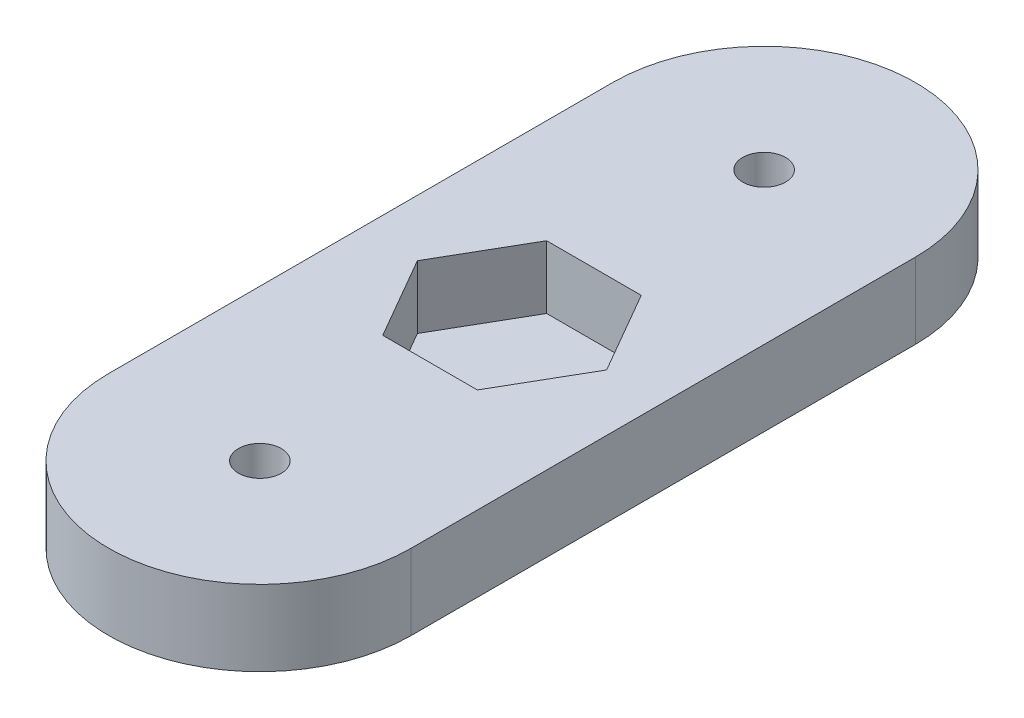
SolidWorks part; units mm, degrees
material "ABS PC"
ref_plane "Front Plane" through (0, 0, 0) normal (0, 0, 1) x (1, 0, 0)
ref_plane "Top Plane" through (0, 0, 0) normal (0, 1, 0) x (1, 0, 0)
ref_plane "Right Plane" through (0, 0, 0) normal (1, 0, 0) x (0, 0, -1)
sketch "Sketch1" plane through (0, 0, 0) normal (0, 1, 0) x (1, 0, 0)
  line L0 (0, 0) -> (0, 40) construction
  line L1 (-12, 0) -> (-12, 40)
  line L2 (12, 0) -> (12, 40)
  arc A0 (-12, 0) -> (12, 0) centre (0, 0) ccw
  arc A1 (12, 40) -> (-12, 40) centre (0, 40) ccw
  circle A2 centre (0, 40) radius 1.7
  circle A3 centre (0, 0) radius 1.7
  point P3 (0, 20)
  dimension "D2" = 40
  dimension "D3" = 3.4
  dimension "D1" = 24
extrude "Boss-Extrude1" add sketch "Sketch1" along normal blind 6
sketch "Sketch2" plane through (0, 6, 0) normal (0, 1, 0) x (1, 0, 0)
  line L0 (12, 0) -> (12, 40) construction
  line L1 (3.7528, 13.5) -> (7.5056, 20)
  line L2 (7.5056, 20) -> (3.7528, 26.5)
  line L3 (3.7528, 26.5) -> (-3.7528, 26.5)
  line L4 (-3.7528, 26.5) -> (-7.5056, 20)
  line L5 (-7.5056, 20) -> (-3.7528, 13.5)
  line L6 (-3.7528, 13.5) -> (3.7528, 13.5)
  line L7 (-12, 40) -> (-12, 0) construction
  circle A0 centre (0, 20) radius 6.5 construction
  dimension "D1" = 13
  dimension "D2" = 12
  dimension "D3" = 20
  dimension "D4" = 90
extrude "Cut-Extrude1" cut sketch "Sketch2" against normal blind 5
